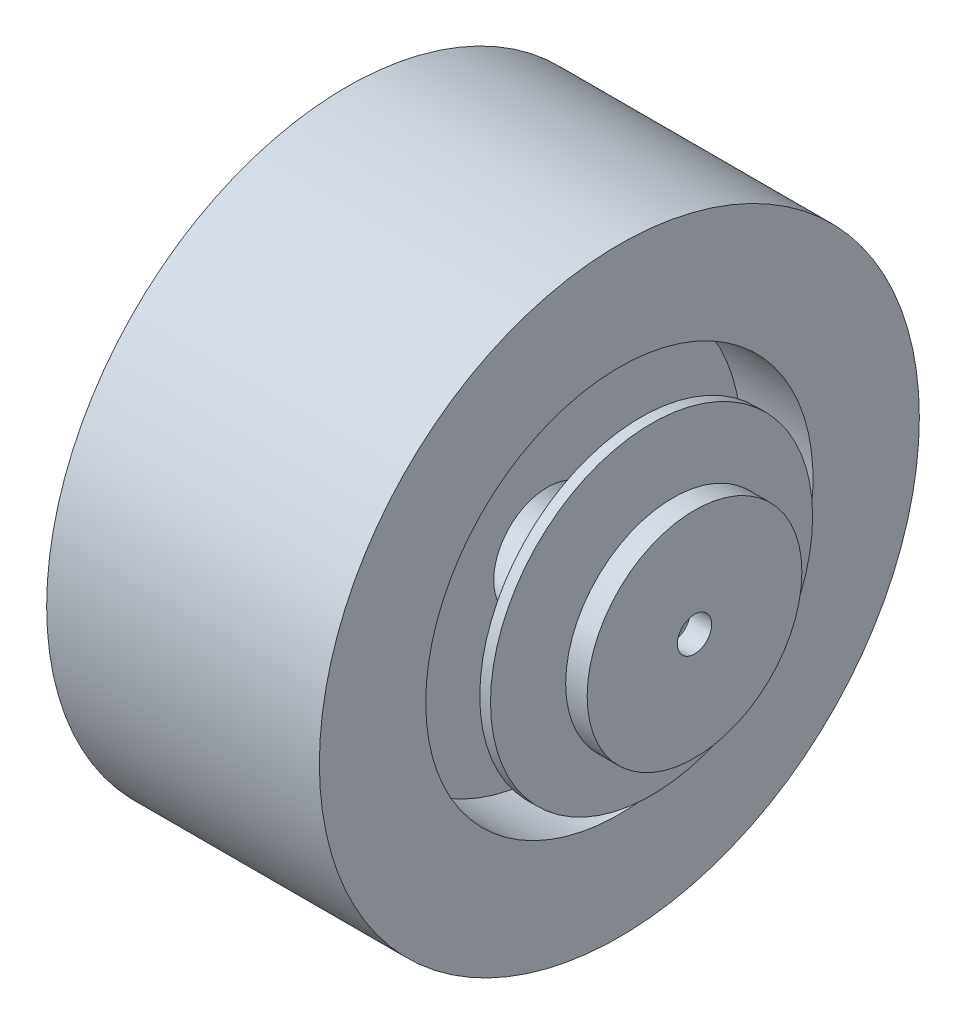
SolidWorks part; units mm, degrees
ref_plane "Front Plane" through (0, 0, 0) normal (0, 0, 1) x (1, 0, 0)
ref_plane "Top Plane" through (0, 0, 0) normal (0, 1, 0) x (1, 0, 0)
ref_plane "Right Plane" through (0, 0, 0) normal (1, 0, 0) x (0, 0, -1)
sketch "Sketch1" plane through (0, 0, 0) normal (0, 0, 1) x (1, 0, 0)
  line L0 (0, -25) -> (0, -139.7)
  line L1 (0, -139.7) -> (-63.5, -139.7)
  line L2 (-63.5, -139.7) -> (-63.5, -90.17)
  line L3 (-63.5, -90.17) -> (-30, -90.17)
  line L4 (-30, -90.17) -> (-30, -25)
  line L5 (-30, -25) -> (0, -25)
  line L6 (-62.8571, 0) -> (53.4694, 0) construction
  dimension "D1" = 25
  dimension "D2" = 139.7
  dimension "D3" = 90.17
  dimension "D4" = 63.5
  dimension "D5" = 30
revolve "Revolve1" add sketch "Sketch1" angle 360 about L6
mirror "Mirror1" about plane through (0, 0, 0) normal (1, 0, 0) of "Revolve1"
sketch "Sketch2" plane through (63.5, 0, 0) normal (1, 0, 0) x (0, 0, -1)
  circle A0 centre (0, 0) radius 75
  dimension "D1" = 150
extrude "Boss-Extrude1" add sketch "Sketch2" along normal blind 5 from offset 10 separate body
sketch "Sketch3" plane through (78.5, 0, 0) normal (1, 0, 0) x (0, 0, -1)
  circle A0 centre (0, 0) radius 50
  dimension "D1" = 100
extrude "Boss-Extrude2" add sketch "Sketch3" along normal blind 10 from offset 10 separate body
sketch "Sketch4" plane through (98.5, 0, 0) normal (1, 0, 0) x (0, 0, -1)
  circle A0 centre (0, 0) radius 8
  dimension "D1" = 16
extrude "Cut-Extrude1" cut sketch "Sketch4" against normal through all
